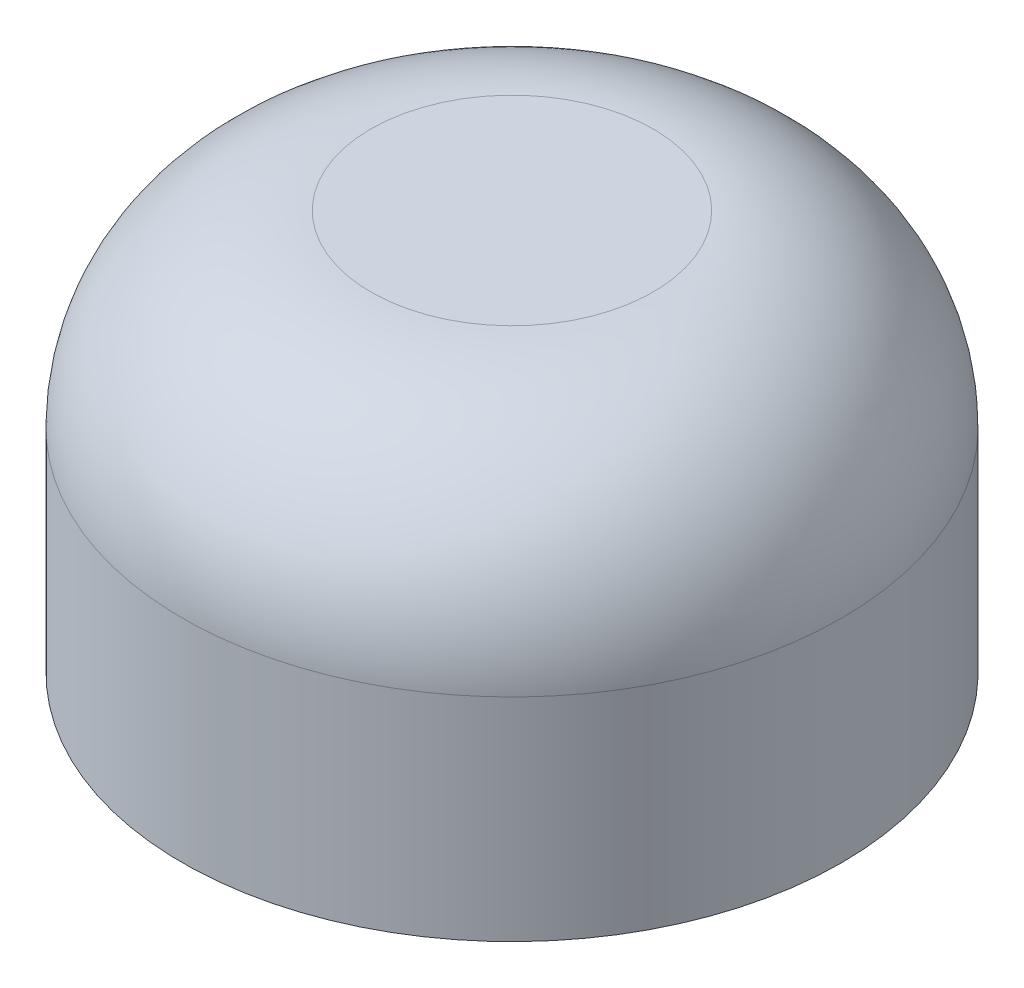
SolidWorks part; units mm, degrees
ref_plane "Piano frontale" through (0, 0, 0) normal (0, 0, 1) x (1, 0, 0)
ref_plane "Piano superiore" through (0, 0, 0) normal (0, 1, 0) x (1, 0, 0)
ref_plane "Piano destro" through (0, 0, 0) normal (1, 0, 0) x (0, 0, -1)
sketch "Schizzo1" plane through (0, 0, 0) normal (0, 0, 1) x (1, 0, 0)
  line L6 (0, 0) -> (1.5, 0)
  line L7 (1.5, 0) -> (1.5, -2.5)
  line L8 (1.5, -2.5) -> (3.5, -2.5)
  line L9 (3.5, -2.5) -> (3.5, -0.25)
  line L10 (1.5, 1.75) -> (0, 1.75)
  line L11 (0, 1.75) -> (0, 0)
  arc A0 (3.5, -0.25) -> (1.5, 1.75) centre (1.5, -0.25) ccw
  dimension "D5" = 2
  dimension "D1" = 1.5
  dimension "D2" = 2
  dimension "D3" = 2.5
  dimension "D4" = 1.75
revolve "Rivoluzione1" add sketch "Schizzo1" angle 360 about L11
